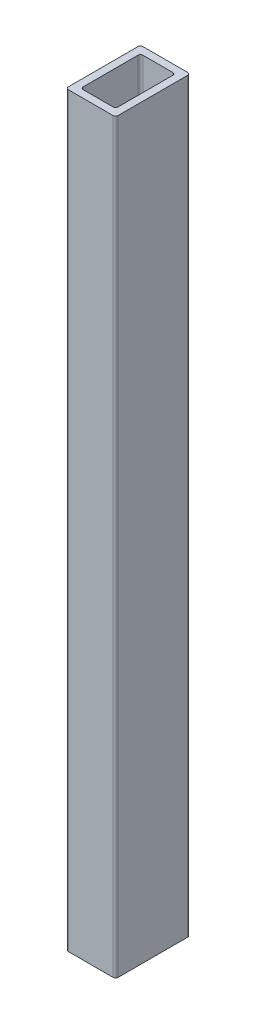
SolidWorks part; units mm, degrees
ref_plane "Front Plane" through (0, 0, 0) normal (0, 0, 1) x (1, 0, 0)
ref_plane "Top Plane" through (0, 0, 0) normal (0, 1, 0) x (1, 0, 0)
ref_plane "Right Plane" through (0, 0, 0) normal (1, 0, 0) x (0, 0, -1)
sketch "Sketch1" plane through (0, 0, 0) normal (0, 1, 0) x (1, 0, 0)
  line L1 (-45, -75) -> (45, -75)
  line L2 (-50, -70) -> (-50, 70)
  line L3 (-45, 75) -> (45, 75)
  line L4 (50, -70) -> (50, 70)
  line L5 (-50, -75) -> (50, 75) construction
  line L6 (-50, 75) -> (50, -75) construction
  line L7 (-30, -60) -> (30, -60)
  line L8 (-35, -55) -> (-35, 55)
  line L9 (-30, 60) -> (30, 60)
  line L10 (35, -55) -> (35, 55)
  line L11 (-35, -60) -> (35, 60) construction
  line L12 (-35, 60) -> (35, -60) construction
  arc A0 (-45, -75) -> (-50, -70) centre (-45, -70) cw
  arc A1 (-35, -55) -> (-30, -60) centre (-30, -55) ccw
  arc A2 (35, -55) -> (30, -60) centre (30, -55) cw
  arc A3 (45, -75) -> (50, -70) centre (45, -70) ccw
  arc A4 (35, 55) -> (30, 60) centre (30, 55) ccw
  arc A5 (50, 70) -> (45, 75) centre (45, 70) ccw
  arc A6 (-30, 60) -> (-35, 55) centre (-30, 55) ccw
  arc A7 (-50, 70) -> (-45, 75) centre (-45, 70) cw
  point P0 (0, 0)
  point P6 (0, 0)
  dimension "D5" = 5
  dimension "D1" = 100
  dimension "D2" = 150
  dimension "D3" = 15
  dimension "D4" = 15
extrude "Boss-Extrude1" add sketch "Sketch1" along normal blind 1500
